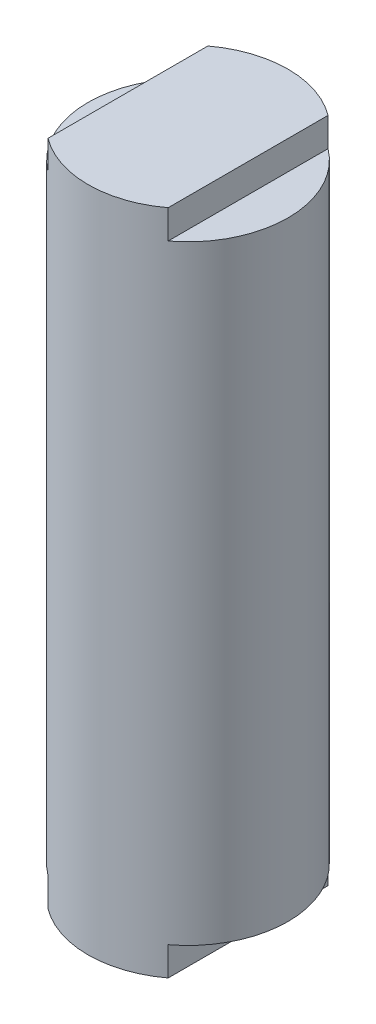
SolidWorks part; units mm, degrees
ref_plane "Front Plane" through (0, 0, 0) normal (0, 0, 1) x (1, 0, 0)
ref_plane "Top Plane" through (0, 0, 0) normal (0, 1, 0) x (1, 0, 0)
ref_plane "Right Plane" through (0, 0, 0) normal (1, 0, 0) x (0, 0, -1)
sketch "Sketch2" plane through (0, 0, 0) normal (0, 1, 0) x (1, 0, 0)
  circle A0 centre (0, 0) radius 26.415
  dimension "D1" = 52.83
extrude "Extrude1" add sketch "Sketch2" along normal mid plane 176.2125
sketch "Sketch3" plane through (0, 0, 0) normal (0, 0, 1) x (1, 0, 0)
  line L1 (26.415, 88.1063) -> (15.874, 88.1063)
  line L2 (26.415, 88.1063) -> (26.415, 80.4862)
  line L3 (26.415, 80.4862) -> (15.874, 80.4862)
  line L4 (15.874, 88.1063) -> (15.874, 80.4862)
  dimension "D1" = 10.541
  dimension "D2" = 7.62
extrude "Extrude2" cut sketch "Sketch3" against normal through all and the other way through all
mirror "Mirror1" about plane through (0, 0, 0) normal (1, 0, 0) of "Extrude2"
mirror "Mirror2" about plane through (0, 0, 0) normal (0, 1, 0) of "Mirror1", "Extrude2"
